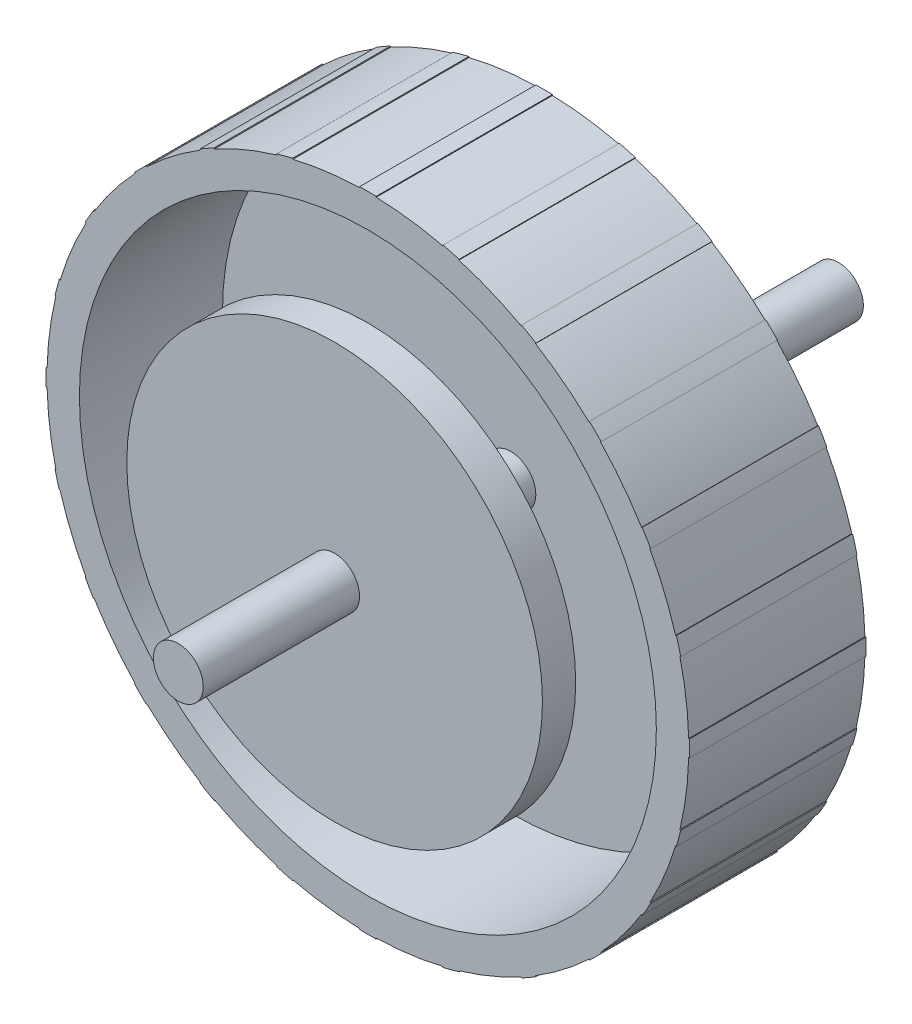
SolidWorks part; units mm, degrees
ref_plane "Front Plane" through (0, 0, 0) normal (0, 0, 1) x (1, 0, 0)
ref_plane "Top Plane" through (0, 0, 0) normal (0, 1, 0) x (1, 0, 0)
ref_plane "Right Plane" through (0, 0, 0) normal (1, 0, 0) x (0, 0, -1)
sketch "Sketch1" plane through (0, 0, 0) normal (0, 0, 1) x (1, 0, 0)
  line L0 (0, 19.3) -> (0, -19.3) construction
  line L1 (-19.3, 0) -> (19.3, 0) construction
  circle A0 centre (0, 0) radius 19.3
  dimension "D1" = 38.6
extrude "Boss-Extrude1" add sketch "Sketch1" along normal blind 10.6
sketch "Sketch3" plane through (0, 0, 10.6) normal (0, 0, 1) x (1, 0, 0)
  line L0 (0, 0) -> (0.5, 19.3435) construction
  line L1 (0, 0) -> (-0.5, 19.3435) construction
  line L2 (0, 0) -> (0, 19.35)
  line L3 (-0.5, 19.3435) -> (0.5, 19.3435) construction
  line L4 (-0.5, 19.3435) -> (-0.4987, 19.2936)
  line L5 (0.5, 19.3435) -> (0.4987, 19.2936)
  arc A0 (0.5, 19.3435) -> (-0.5, 19.3435) centre (0, 0) ccw
  circle A1 centre (0, 0) radius 19.3 construction
  arc A2 (0.4987, 19.2936) -> (-0.4987, 19.2936) centre (0, 0) ccw
  point P3 (0, 19.3435)
  dimension "D1" = 0.05
  dimension "D2" = 1
extrude "Boss-Extrude3" add sketch "Sketch3" against normal through all contours A0 L4 A2 L5
sketch "Sketch8" plane through (0, 0, 10.6) normal (0, 0, 1) x (1, 0, 0)
  circle A0 centre (0, 0) radius 17.35
  arc A2 (0.5, 19.3435) -> (-0.5, 19.3435) centre (0, 0) ccw construction
  dimension "D1" = 2
extrude "Cut-Extrude2" cut sketch "Sketch8" against normal offset from surface (8.6 mm away) 2 up to face at (0, 9.6718, 0)
pattern_circular "CirPattern1" count 24 over 360 about axis through (0, 0, 0) along (0, 0, 1) of "Boss-Extrude3"
sketch "Sketch5" plane through (0, 0, 0) normal (0, 1, 0) x (1, 0, 0)
  line L0 (0, 0) -> (4, 0)
  line L1 (4.5118, 0) -> (0.4987, 0) construction
  line L2 (4, 0) -> (2.95, 1.05)
  line L3 (2.95, 1.05) -> (2.95, 8)
  line L4 (2.95, 8) -> (0, 8)
  line L5 (0, 8) -> (0, 0)
  dimension "D1" = 2.95
  dimension "D2" = 4
  dimension "D3" = 45
  dimension "D4" = 8
revolve "Revolve1" add sketch "Sketch5" angle 360 about L5
sketch "Sketch6" plane through (0, 0, -8) normal (0, 0, -1) x (-1, 0, 0)
  line L0 (0.95, 1.1608) -> (0.95, -1.1608)
  line L1 (0.95, 0) -> (-1.5, 0) construction
  arc A0 (0.95, 1.1608) -> (0.95, -1.1608) centre (0, 0) ccw
  circle A1 centre (0, 0) radius 1.5 construction
  dimension "D1" = 3
  dimension "D2" = 2.45
extrude "Boss-Extrude4" add sketch "Sketch6" along normal blind 9.7
sketch "Sketch7" plane through (0, 0, 0) normal (0, 0, -1) x (-1, 0, 0)
  line L0 (0, 0) -> (1.1414, 16.0595) construction
  line L1 (0, 0) -> (4.101, 15.5689) construction
  line L2 (1.1414, 16.0595) -> (0.95, 13.3663)
  line L3 (0.95, 13.3663) -> (0.95, 1.1608) construction
  line L4 (4.101, 15.5689) -> (3.4133, 12.958)
  arc A0 (4.101, 15.5689) -> (1.1414, 16.0595) centre (0, 0) ccw
  arc A1 (3.4133, 12.958) -> (0.95, 13.3663) centre (0, 0) ccw
  arc A3 (9.2149, 16.9581) -> (5.4753, 18.5071) centre (0, 0) ccw construction
  dimension "D1" = 2.7
  dimension "D2" = 3.2
  dimension "D3" = 3
extrude "Cut-Extrude1" cut sketch "Sketch7" against normal through all
sketch "Sketch9" plane through (0, 0, 0) normal (0, 0, -1) x (-1, 0, 0)
  line L0 (3.4133, 12.958) -> (4.101, 15.5689) construction
  line L1 (3.4133, 12.958) -> (4.101, 15.5689)
  line L2 (4.101, 15.5689) -> (5.0597, 15.2843)
  line L3 (5.0597, 15.2843) -> (0, 0) construction
  line L4 (5.0597, 15.2843) -> (4.2112, 12.7211) construction
  arc A0 (3.4133, 12.958) -> (0.95, 13.3663) centre (0, 0) ccw construction
  arc A1 (4.101, 15.5689) -> (1.1414, 16.0595) centre (0, 0) ccw construction
  arc A2 (3.4133, 12.958) -> (0.95, 13.3663) centre (0, 0) ccw construction
  arc A3 (4.101, 15.5689) -> (1.1414, 16.0595) centre (0, 0) ccw construction
  arc A4 (5.0597, 15.2843) -> (1.1414, 16.0595) centre (0, 0) ccw
  arc A5 (4.2112, 12.7211) -> (0.95, 13.3663) centre (0, 0) ccw
  arc A6 (5.0597, 15.2843) -> (4.2112, 12.7211) centre (4.6354, 14.0027) cw
  dimension "D1" = 1
extrude "Boss-Extrude5" add sketch "Sketch9" along normal blind 0.1 contours A6 L2 L1 A5
pattern_circular "CirPattern2" count 3 over 360 about axis through (0, 0, 0) along (0, 0, 1) of "Cut-Extrude1", "Boss-Extrude5"
sketch "Sketch10" plane through (0, 0, 2) normal (0, 0, 1) x (1, 0, 0)
  line L0 (-19.3, 0) -> (19.3, 0) construction
  circle A0 centre (0, 0) radius 1.5
  dimension "D1" = 3
extrude "Boss-Extrude6" add sketch "Sketch10" along normal blind 20
sketch "Sketch11" plane through (0, 0, 10.6) normal (0, 0, 1) x (1, 0, 0)
  circle A0 centre (0, 0) radius 12.5
  dimension "D1" = 25
extrude "Boss-Extrude7" add sketch "Sketch11" along normal blind 2
